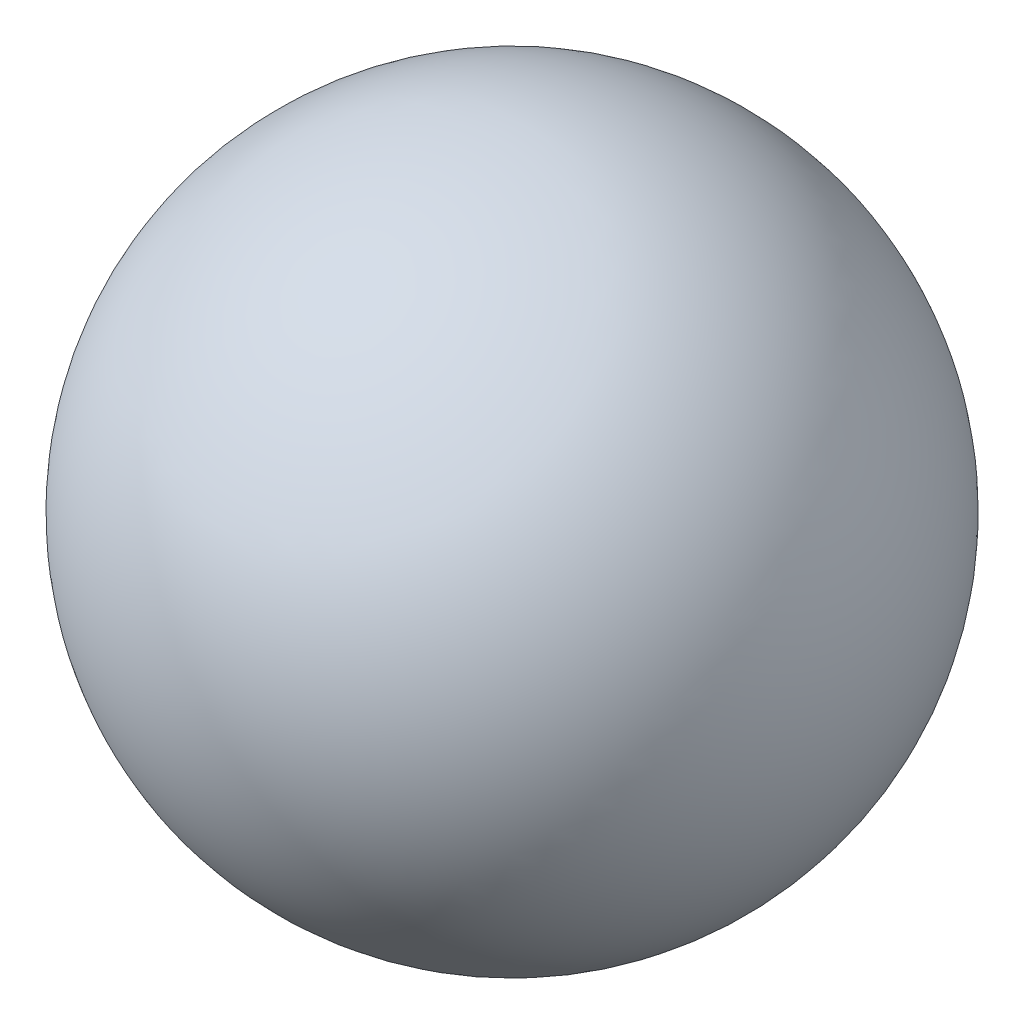
SolidWorks part; units mm, degrees
ref_plane "前视基准面" through (0, 0, 0) normal (0, 0, 1) x (1, 0, 0)
ref_plane "上视基准面" through (0, 0, 0) normal (0, 1, 0) x (1, 0, 0)
ref_plane "右视基准面" through (0, 0, 0) normal (1, 0, 0) x (0, 0, -1)
sketch "草图1" plane through (0, 0, 0) normal (0, 1, 0) x (1, 0, 0)
  line L0 (0, -2) -> (0, 2)
  arc A0 (0, -2) -> (0, 2) centre (0, 0) ccw
  dimension "D1" = 4
revolve "旋转1" add sketch "草图1" angle 360 about L0
